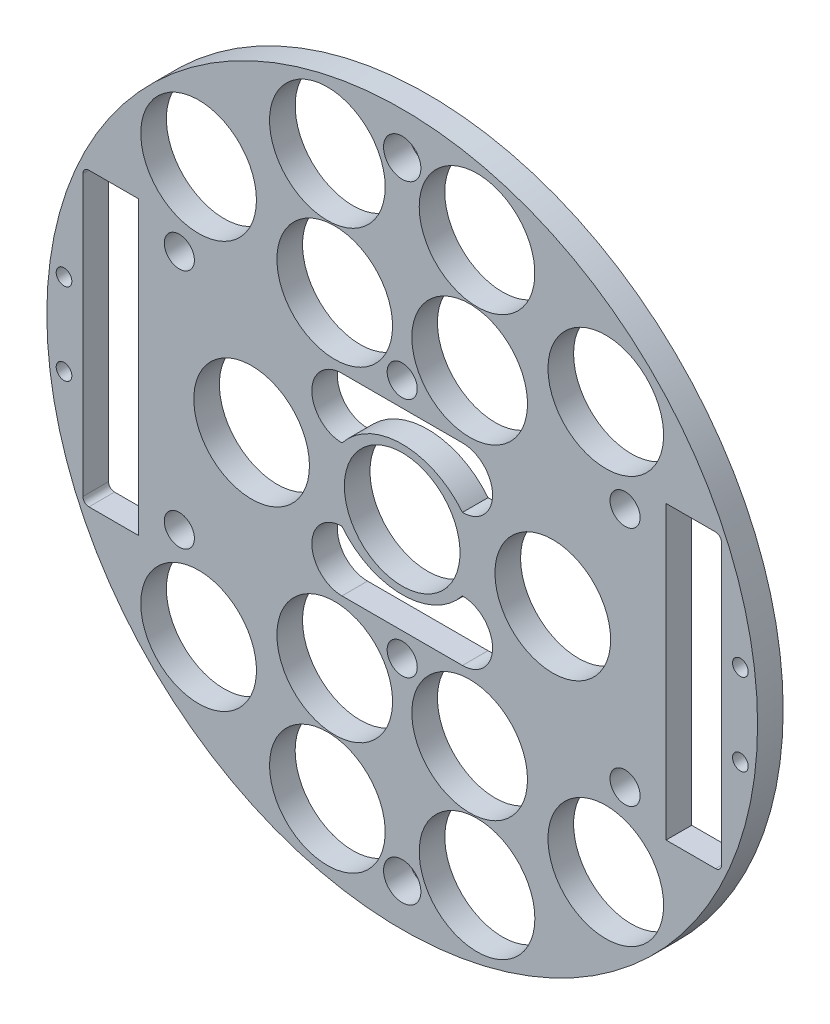
SolidWorks part; units mm, degrees
ref_plane "Front Plane" through (0, 0, 0) normal (0, 0, 1) x (1, 0, 0)
ref_plane "Top Plane" through (0, 0, 0) normal (0, 1, 0) x (1, 0, 0)
ref_plane "Right Plane" through (0, 0, 0) normal (1, 0, 0) x (0, 0, -1)
sketch "Sketch1" plane through (0, 0, 0) normal (0, 0, 1) x (1, 0, 0)
  line L0 (0, 0) -> (-82.1241, 0) construction
  line L1 (0, 0) -> (0, 95.6219) construction
  line L3 (-68.3369, 30.734) -> (-55.6369, 30.734)
  line L5 (-68.3369, -30.734) -> (-55.6369, -30.734)
  line L6 (-55.6369, 30.734) -> (-55.6369, -30.734)
  line L7 (68.3369, -30.734) -> (55.6369, -30.734)
  line L8 (68.3369, 30.734) -> (55.6369, 30.734)
  line L9 (55.6369, 30.734) -> (55.6369, -30.734)
  arc A0 (-68.3369, -30.734) -> (68.3369, -30.734) centre (0, 0) ccw
  circle A1 centre (-45.466, 11.049) radius 1.651
  circle A2 centre (-20.0673, 10.795) radius 1.651
  circle A3 centre (-20.0673, -10.795) radius 1.651
  circle A4 centre (-45.466, -11.049) radius 1.651
  circle A5 centre (45.466, -11.049) radius 1.651
  circle A6 centre (20.0673, -10.795) radius 1.651
  circle A7 centre (20.0673, 10.795) radius 1.651
  circle A8 centre (45.466, 11.049) radius 1.651
  arc A9 (68.3369, 30.734) -> (-68.3369, 30.734) centre (0, 0) ccw
  dimension "D2" = 3.302
  dimension "D3" = 3.302
  dimension "D4" = 25.4
  dimension "D5" = 10.795
  dimension "D10" = 45.466
  dimension "D6" = 61.468
  dimension "D7" = 12.7
  dimension "D8" = 74.93
  dimension "D9" = 74.93
  dimension "D11" = 30.734
extrude "Boss-Extrude2" add sketch "Sketch1" along normal blind 5.3975
sketch "Sketch3" [suppressed] plane through (0, 0, 0) normal (0, 0, -1) x (-1, 0, 0)
  line L0 (0, 0) -> (0, -116.2908) construction
  line L1 (0, 0) -> (-153.8039, 0) construction
  line L2 (0, 0) -> (15.2681, -56.9814) construction
  line L3 (0, 0) -> (15.2302, -26.3795) construction
  circle A1 centre (0, -13.208) radius 12.1285
  circle A2 centre (0, 13.208) radius 12.1285
  circle A4 centre (-43.1052, -43.1052) radius 12.1285
  circle A6 centre (19.05, -32.9956) radius 12.1285
  circle A7 centre (19.05, 32.9956) radius 12.1285
  circle A8 centre (-43.1052, 43.1052) radius 12.1285
  circle A11 centre (43.1052, 43.1052) radius 12.1285
  circle A12 centre (-19.05, 32.9956) radius 12.1285
  circle A13 centre (-19.05, -32.9956) radius 12.1285
  circle A14 centre (43.1052, -43.1052) radius 12.1285
  point P36 (0, 0)
  point P53 (0, 0)
  point P55 (0, 0)
  dimension "D1" = 24.257
  dimension "D2" = 24.257
  dimension "D4" = 15
  dimension "D6" = 0
  dimension "D8" = 24.257
  dimension "D9" = 30
  dimension "D10" = 13.208
  dimension "D11" = 13.208
sketch "Sketch4" plane through (0, 0, 0) normal (0, 0, -1) x (-1, 0, 0)
  line L0 (-68.3369, -30.734) -> (-67.3209, -30.734)
  line L1 (-68.3369, -30.734) -> (-55.6369, -30.734) construction
  line L2 (-67.3209, -30.734) -> (-67.3209, 30.734)
  line L3 (-55.6369, 30.734) -> (-68.3369, 30.734) construction
  line L4 (-67.3209, 30.734) -> (-68.3369, 30.734)
  line L5 (0, 0) -> (0, 87.9765) construction
  line L6 (-55.6369, -30.734) -> (-55.6369, 30.734) construction
  line L7 (67.3209, 30.734) -> (68.3369, 30.734)
  line L8 (68.3369, -30.734) -> (67.3209, -30.734)
  line L9 (67.3209, -30.734) -> (67.3209, 30.734)
  arc A0 (68.3369, -30.734) -> (68.3369, 30.734) centre (0, 0) ccw
  arc A1 (-68.3369, 30.734) -> (-68.3369, -30.734) centre (0, 0) ccw
  dimension "D1" = 11.684
extrude "Boss-Extrude3" add sketch "Sketch4" against normal up to surface (5.3975 mm away) up to face at (18.4163, 10.795, 5.3975)
fillet "Fillet1" radius 1.27 4 edges at (67.3209, 30.734, 2.6987) (67.3209, -30.734, 2.6987) (-67.3209, 30.734, 2.6987) (-67.3209, -30.734, 2.6987)
sketch "Sketch5" plane through (0, 0, 0) normal (0, 0, -1) x (-1, 0, 0)
  line L1 (16.7319, 15.0155) -> (52.8378, 15.0155)
  line L2 (16.7319, 15.0155) -> (16.7319, -15.7858)
  line L3 (16.7319, -15.7858) -> (52.8378, -15.7858)
  line L4 (52.8378, 15.0155) -> (52.8378, -15.7858)
  line L5 (-50.8098, 17.6836) -> (-14.8513, 17.6836)
  line L6 (-50.8098, 17.6836) -> (-50.8098, -15.7858)
  line L7 (-50.8098, -15.7858) -> (-14.8513, -15.7858)
  line L8 (-14.8513, 17.6836) -> (-14.8513, -15.7858)
extrude "Boss-Extrude4" add sketch "Sketch5" against normal up to surface (5.3975 mm away) up to face at (-63.0905, 0, 5.3975)
sketch "Sketch6" plane through (0, 0, 0) normal (0, 0, -1) x (-1, 0, 0)
  line L0 (0, 0) -> (-47.3474, 0) construction
  line L1 (0, 0) -> (0, 51.5912) construction
  circle A0 centre (-34.29, 15.24) radius 5
  circle A1 centre (34.29, 15.24) radius 5
  circle A2 centre (-34.29, -15.24) radius 5
  circle A3 centre (34.29, -15.24) radius 5
  dimension "D1" = 68.58
  dimension "D2" = 68.58
  dimension "D3" = 30.48
  dimension "D4" = 30.48
  dimension "D5" = 10
  dimension "D7" = 10
extrude "Cut-Extrude3" [suppressed] cut sketch "Sketch6" against normal through all
extrude "Cut-Extrude4" cut sketch "Sketch7" along normal through all both
sketch "Sketch7" plane through (30.0878, -133.0829, 0) normal (0, 0, 1) x (-0.0084, -1, 0)
  line L0 (-132.559, -31.3134) -> (-132.559, 57.8454) construction
  line L1 (-132.559, -31.3134) -> (-222.516, -31.3134) construction
  circle A0 centre (-157.959, 14.4066) radius 3.175
  circle A1 centre (-173.199, -31.3134) radius 3.175
  circle A3 centre (-157.959, -77.0334) radius 3.175
  circle A4 centre (-107.159, -77.0334) radius 3.175
  circle A5 centre (-91.919, -31.3134) radius 3.175
  circle A6 centre (-107.159, 14.4066) radius 3.175
sketch "Sketch8" plane through (0, 0, 0) normal (0, 0, -1) x (-1, 0, 0)
  circle A0 centre (-45.8215, 24.7494) radius 4.445
  circle A1 centre (-0.2312, 40.3731) radius 4.445
  circle A2 centre (45.6153, 25.5179) radius 4.445
  circle A3 centre (46.0423, -25.2803) radius 4.445
  circle A4 centre (0.452, -40.904) radius 4.445
  circle A5 centre (-45.3945, -26.0488) radius 4.445
  circle A6 centre (-45.8215, 24.7494) radius 3.175 construction
  circle A7 centre (-0.2312, 40.3731) radius 3.175 construction
  circle A8 centre (45.6153, 25.5179) radius 3.175 construction
  circle A9 centre (46.0423, -25.2803) radius 3.175 construction
  circle A10 centre (0.452, -40.904) radius 3.175 construction
  circle A11 centre (-45.3945, -26.0488) radius 3.175 construction
  dimension "D1" = 1.27
  dimension "D2" = 1.27
  dimension "D3" = 1.27
  dimension "D4" = 1.27
  dimension "D5" = 1.27
  dimension "D6" = 1.27
extrude "Boss-Extrude5" add sketch "Sketch8" against normal up to surface (5.3975 mm away) up to face at (3.4062, 40.3731, 5.3975)
extrude "Cut-Extrude5" cut sketch "Sketch9" against normal through all both and the other way through all
sketch "Sketch9" plane through (31.3134, -132.614, -6.35) normal (0, 0, 1) x (0, -1, 0)
  line L0 (-132.614, -31.3134) -> (-132.614, 57.8454) construction
  line L1 (-132.614, -31.3134) -> (-222.516, -31.3134) construction
  circle A0 centre (-158.014, 14.4066) radius 3.175
  circle A1 centre (-173.254, -31.3134) radius 3.175
  circle A3 centre (-158.014, -77.0334) radius 3.175
  circle A4 centre (-107.214, -77.0334) radius 3.175
  circle A5 centre (-91.974, -31.3134) radius 3.175
  circle A6 centre (-107.214, 14.4066) radius 3.175
extrude "Cut-Extrude6" cut sketch "Sketch10" against normal blind 16.51
sketch "Sketch10" plane through (31.3134, -132.559, 6.35) normal (0, 0, 1) x (0, -1, 0)
  line L0 (-132.559, -31.3134) -> (-132.559, -98.8476) construction
  line L1 (-132.559, -31.3134) -> (-20.2053, -31.3134) construction
  circle A1 centre (-198.599, -31.3134) radius 1.651
  circle A2 centre (-66.519, -31.3134) radius 1.651
  circle A3 centre (-132.559, -82.1134) radius 1.651
  circle A4 centre (-132.559, 19.4866) radius 1.651
extrude "Cut-Extrude8" cut sketch "Sketch12" against normal through all both and the other way through all
sketch "Sketch12" plane through (54.1415, -7.5982, -9.525) normal (0, 0, -1) x (-1, 0, 0)
  line L0 (54.1415, 7.5982) -> (54.1415, 115.9369) construction
  line L1 (54.1415, 7.5982) -> (196.092, 7.5982) construction
  circle A1 centre (11.2155, 50.5242) radius 12.192
  circle A2 centre (38.3638, 66.481) radius 12.192
  circle A3 centre (39.9175, 41.8882) radius 12.192
  circle A10 centre (54.1415, 7.5982) radius 12.192
  circle A11 centre (69.9191, 66.481) radius 12.192
  circle A12 centre (68.3655, 41.8882) radius 12.192
  circle A14 centre (97.0675, 50.5242) radius 12.192
  circle A16 centre (68.3655, -26.6918) radius 12.192
  circle A17 centre (97.0675, -35.3278) radius 12.192
  circle A18 centre (69.9191, -51.2847) radius 12.192
  circle A19 centre (38.3638, -51.2847) radius 12.192
  circle A20 centre (11.2155, -35.3278) radius 12.192
  circle A21 centre (39.9175, -26.6918) radius 12.192
sketch "Sketch14" plane through (0, 0, 0) normal (0, 0, -1) x (-1, 0, 0)
  line L0 (0, 20.32) -> (0, 26.3732) construction
  line L1 (19.558, 0) -> (33.6126, 0) construction
  line L2 (-12.7, 20.32) -> (12.7, 20.32)
  line L3 (-12.7, -20.32) -> (12.7, -20.32)
  circle A0 centre (-31.75, 0) radius 12.192
  arc A1 (-12.7, 20.32) -> (-12.7, 7.62) centre (-12.7, 13.97) ccw
  arc A2 (12.7, 20.32) -> (12.7, 7.62) centre (12.7, 13.97) cw
  circle A3 centre (31.75, 0) radius 12.192
  arc A4 (12.7, -20.32) -> (12.7, -7.62) centre (12.7, -13.97) ccw
  arc A5 (-12.7, -20.32) -> (-12.7, -7.62) centre (-12.7, -13.97) cw
  arc A6 (-12.7, 7.62) -> (12.7, 7.62) centre (0, -2.46) cw
  arc A7 (-12.7, -7.62) -> (12.7, -7.62) centre (0, 2.46) ccw
  dimension "D1" = 24.384
  dimension "D3" = 12.7
  dimension "D2" = 31.75
  dimension "D4" = 12.7
  dimension "D5" = 13.97
  dimension "D6" = 13.97
extrude "Cut-Extrude10" cut sketch "Sketch14" against normal blind 38.862
sketch "Sketch15" plane through (0, 0, 0) normal (0, 0, -1) x (-1, 0, 0)
  line L0 (0, 0) -> (107.9945, 0) construction
  circle A0 centre (0, -66.04) radius 3.937
  circle A1 centre (0, 66.04) radius 3.937
  dimension "D1" = 7.874
  dimension "D2" = 66.04
extrude "Cut-Extrude11" cut sketch "Sketch15" against normal blind 21.59
extrude "Cut-Extrude12" cut sketch "Sketch16" against normal blind 150.876
sketch "Sketch16" plane through (-30.092, 4.0835, -57.7215) normal (0, 0, -1) x (-1, 0, 0)
  circle A0 centre (-101.396, -12.7195) radius 1.651
  circle A1 centre (-101.396, 4.5525) radius 1.651
  circle A2 centre (41.212, -12.7195) radius 1.651
  circle A3 centre (41.212, 4.5525) radius 1.651
extrude "Cut-Extrude13" cut sketch "Sketch17" against normal blind 48.768 and the other way blind 103.378
sketch "Sketch17" plane through (-30.092, 4.0835, -46.9265) normal (0, 0, 1) x (1, 0, 0)
  line L0 (30.092, -4.0835) -> (148.6336, -4.0835) construction
  line L1 (30.092, -4.0835) -> (30.092, 90.452) construction
  circle A0 centre (-16.898, 21.3165) radius 3.175
  circle A1 centre (77.082, 21.3165) radius 3.175
  circle A2 centre (30.092, 21.3165) radius 3.175
  circle A4 centre (77.082, -29.4835) radius 3.175
  circle A5 centre (30.092, -29.4835) radius 3.175
  circle A6 centre (-16.898, -29.4835) radius 3.175
